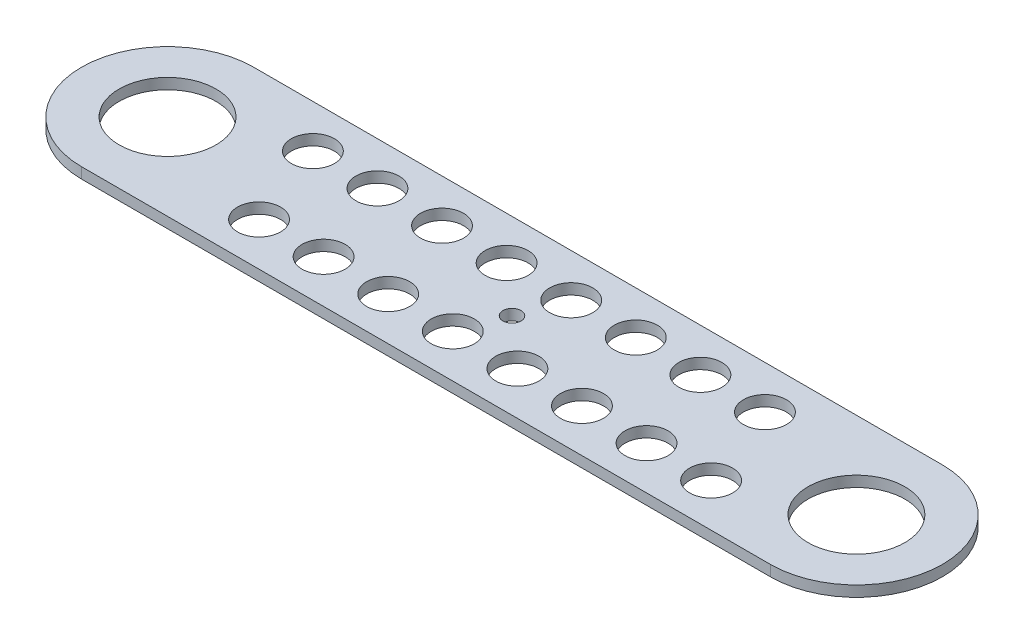
SolidWorks part; units mm, degrees
ref_plane "Front" through (0, 0, 0) normal (0, 0, 1) x (1, 0, 0)
ref_plane "Top" through (0, 0, 0) normal (0, 1, 0) x (1, 0, 0)
ref_plane "Right" through (0, 0, 0) normal (1, 0, 0) x (0, 0, -1)
sketch "Sketch1" plane through (0, 0, 0) normal (0, 1, 0) x (1, 0, 0)
  line L0 (0, 0) -> (203.2, 0) construction
  line L1 (0, 0) -> (203.2, 0) construction
  line L2 (0, 25.4) -> (203.2, 25.4)
  line L3 (0, -25.4) -> (203.2, -25.4)
  circle A0 centre (0, 0) radius 14.2875
  circle A1 centre (203.2, 0) radius 14.2875
  arc A2 (0, 25.4) -> (0, -25.4) centre (0, 0) ccw
  arc A3 (203.2, -25.4) -> (203.2, 25.4) centre (203.2, 0) ccw
  point P5 (101.6, 0)
  point P10 (101.6, -25.4)
  dimension "D1" = 28.575
  dimension "D2" = 28.575
  dimension "D3" = 203.2
  dimension "D4" = 50.8
extrude "Boss-Extrude1" add sketch "Sketch1" along normal blind 3.175
sketch "Sketch2" plane through (0, 3.175, 0) normal (0, 1, 0) x (1, 0, 0)
  line L0 (0, 0) -> (203.2, 0) construction
  circle A0 centre (101.6, 0) radius 2.667
  dimension "D1" = 5.334
extrude "Cut-Extrude1" cut sketch "Sketch2" against normal up to next
sketch "Sketch3" plane through (0, 3.175, 0) normal (0, 1, 0) x (1, 0, 0)
  line L0 (203.2, 0) -> (228.6, 0) construction
  line L1 (0, 0) -> (-25.4, 0) construction
  line L2 (-25.4, 0) -> (-25.4, 25.4) construction
  arc A0 (203.2, -25.4) -> (203.2, 25.4) centre (203.2, 0) ccw construction
  arc A1 (0, 25.4) -> (0, -25.4) centre (0, 0) ccw construction
  dimension "D1" = 25.4
sketch "Sketch4" plane through (0, 0, 0) normal (0, -1, 0) x (1, 0, 0)
  line L0 (30.1625, -25.4) -> (30.1625, -12.7) construction
  line L1 (203.2, -25.4) -> (0, -25.4) construction
  line L2 (39.6875, 25.4) -> (39.6875, 12.7) construction
  line L3 (0, 25.4) -> (203.2, 25.4) construction
  line L4 (30.1625, -12.7) -> (49.2125, -12.7) construction
  line L5 (39.6875, -12.7) -> (39.6875, 12.7) construction
  line L6 (30.1625, -12.7) -> (0, 0) construction
  line L7 (173.0375, 12.7) -> (203.2, 0) construction
  circle A0 centre (30.1625, -12.7) radius 6.35
  circle A1 centre (49.2125, -12.7) radius 6.35
  circle A2 centre (68.2625, -12.7) radius 6.35
  circle A3 centre (87.3125, -12.7) radius 6.35
  circle A4 centre (106.3625, -12.7) radius 6.35
  circle A5 centre (125.4125, -12.7) radius 6.35
  circle A6 centre (144.4625, -12.7) radius 6.35
  circle A7 centre (163.5125, -12.7) radius 6.35
  circle A8 centre (39.6875, 12.7) radius 6.35
  circle A9 centre (58.7375, 12.7) radius 6.35
  circle A10 centre (77.7875, 12.7) radius 6.35
  circle A11 centre (96.8375, 12.7) radius 6.35
  circle A12 centre (115.8875, 12.7) radius 6.35
  circle A13 centre (134.9375, 12.7) radius 6.35
  circle A14 centre (153.9875, 12.7) radius 6.35
  circle A15 centre (173.0375, 12.7) radius 6.35
  dimension "D1" = 12.7
  dimension "D4" = 8
  dimension "D2" = 8
  dimension "D3" = 12.7
extrude "Cut-Extrude2" cut sketch "Sketch4" against normal up to next
